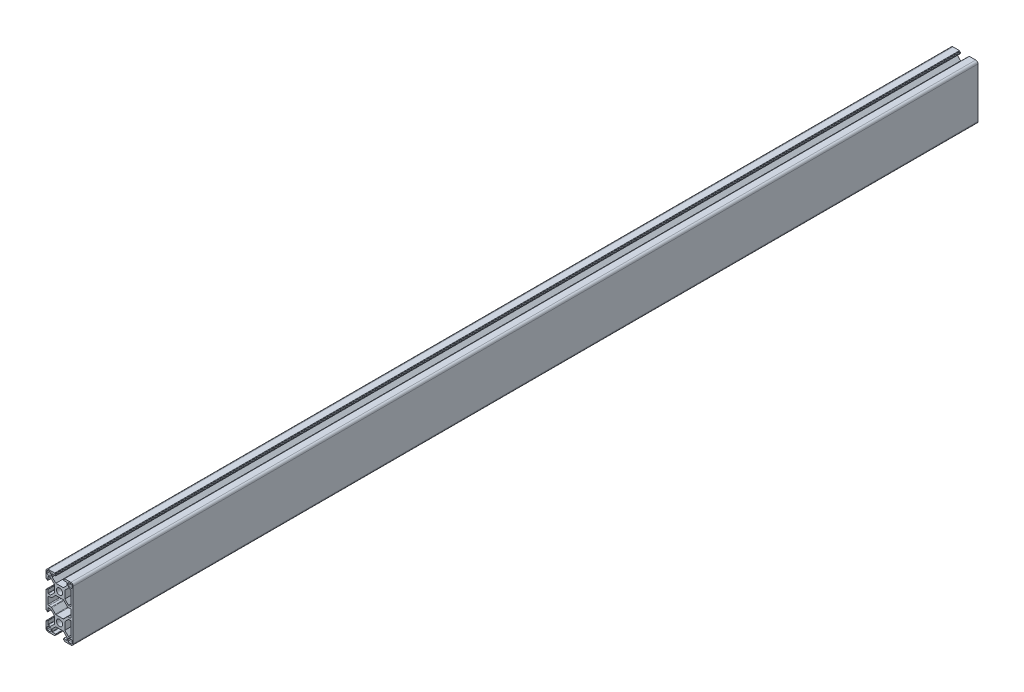
SolidWorks part; units mm, degrees
material "6063 T5"
ref_plane "Спереди" through (0, 0, 0) normal (0, 0, 1) x (1, 0, 0)
ref_plane "Сверху" through (0, 0, 0) normal (0, 1, 0) x (1, 0, 0)
ref_plane "Справа" through (0, 0, 0) normal (1, 0, 0) x (0, 0, -1)
sketch "Эскиз1" plane through (0, 0, 0) normal (0, 0, 1) x (1, 0, 0)
  line L0 (42.4804, 14.8887) -> (42.4804, -45.1113) construction
  line L1 (-15, 8.25) -> (-15, 12.5)
  line L2 (-12.5, 15) -> (-8.25, 15)
  line L3 (8.25, 15) -> (12.5, 15)
  line L4 (15, 12.5) -> (15, 8.25)
  line L5 (12.75, 9.55) -> (10.55, 9.55)
  line L6 (-12.75, 13.75) -> (-10.55, 13.75)
  line L7 (-13.75, 12.75) -> (-13.75, 10.55)
  line L8 (-12.75, 9.55) -> (-10.55, 9.55)
  line L9 (-9.55, 12.75) -> (-9.55, 10.55)
  line L10 (13.75, 12.75) -> (13.75, 10.55)
  line L11 (12.75, 13.75) -> (10.55, 13.75)
  line L12 (9.55, 12.75) -> (9.55, 10.55)
  line L13 (0, 0) -> (0, -30) construction
  line L14 (0, -15) -> (-22.4838, -15) construction
  line L15 (9.55, -42.75) -> (9.55, -40.55)
  line L16 (12.75, -43.75) -> (10.55, -43.75)
  line L17 (13.75, -42.75) -> (13.75, -40.55)
  line L18 (-9.55, -42.75) -> (-9.55, -40.55)
  line L19 (-12.75, -39.55) -> (-10.55, -39.55)
  line L20 (-13.75, -42.75) -> (-13.75, -40.55)
  line L21 (-12.75, -43.75) -> (-10.55, -43.75)
  line L22 (12.75, -39.55) -> (10.55, -39.55)
  line L23 (15, -42.5) -> (15, -38.25)
  line L24 (8.25, -45) -> (12.5, -45)
  line L25 (-12.5, -45) -> (-8.25, -45)
  line L26 (-15, -38.25) -> (-15, -42.5)
  line L27 (-15, -8.25) -> (-15, -21.75)
  line L28 (15, -8.25) -> (15, -21.75)
  line L29 (-12.8, -18.5) -> (-12.8, -11.5)
  line L30 (-11.8, -10.5) -> (-9.4029, -10.5)
  line L31 (-8.6958, -10.2071) -> (-4.5816, -6.0929)
  line L32 (-3.8745, -5.8) -> (3.8745, -5.8)
  line L33 (8.6958, -10.2071) -> (4.5816, -6.0929)
  line L34 (11.8, -10.5) -> (9.4029, -10.5)
  line L35 (12.8, -18.5) -> (12.8, -11.5)
  line L36 (11.8, -19.5) -> (9.4029, -19.5)
  line L37 (8.6958, -19.7929) -> (4.5816, -23.9071)
  line L38 (-3.8745, -24.2) -> (3.8745, -24.2)
  line L39 (-8.6958, -19.7929) -> (-4.5816, -23.9071)
  line L40 (-11.8, -19.5) -> (-9.4029, -19.5)
  line L41 (-20.7769, 14.9626) -> (-20.7769, -45.0374) construction
  line L42 (12.8, -25.6) -> (12.8, -34.4)
  line L43 (15, -24.5) -> (15, -35.5)
  line L44 (12.8, 4.4) -> (12.8, -4.4)
  line L45 (15, 5.5) -> (15, -5.5)
  arc A0 (12.5, 15) -> (15, 12.5) centre (12.5, 12.5) cw
  arc A1 (-15, 12.5) -> (-12.5, 15) centre (-12.5, 12.5) cw
  arc A2 (-13.75, 10.55) -> (-12.75, 9.55) centre (-12.75, 10.55) ccw
  arc A3 (-10.55, 9.55) -> (-9.55, 10.55) centre (-10.55, 10.55) ccw
  arc A4 (-10.55, 13.75) -> (-9.55, 12.75) centre (-10.55, 12.75) cw
  arc A5 (-12.75, 13.75) -> (-13.75, 12.75) centre (-12.75, 12.75) ccw
  arc A6 (10.55, 9.55) -> (9.55, 10.55) centre (10.55, 10.55) cw
  arc A7 (13.75, 10.55) -> (12.75, 9.55) centre (12.75, 10.55) cw
  arc A8 (12.75, 13.75) -> (13.75, 12.75) centre (12.75, 12.75) cw
  arc A9 (10.55, 13.75) -> (9.55, 12.75) centre (10.55, 12.75) ccw
  circle A10 centre (0, 0) radius 3.4
  circle A11 centre (0, -30) radius 3.4
  arc A12 (10.55, -43.75) -> (9.55, -42.75) centre (10.55, -42.75) cw
  arc A13 (12.75, -43.75) -> (13.75, -42.75) centre (12.75, -42.75) ccw
  arc A14 (13.75, -40.55) -> (12.75, -39.55) centre (12.75, -40.55) ccw
  arc A15 (10.55, -39.55) -> (9.55, -40.55) centre (10.55, -40.55) ccw
  arc A16 (-12.75, -43.75) -> (-13.75, -42.75) centre (-12.75, -42.75) cw
  arc A17 (-10.55, -43.75) -> (-9.55, -42.75) centre (-10.55, -42.75) ccw
  arc A18 (-10.55, -39.55) -> (-9.55, -40.55) centre (-10.55, -40.55) cw
  arc A19 (-13.75, -40.55) -> (-12.75, -39.55) centre (-12.75, -40.55) cw
  arc A20 (-15, -42.5) -> (-12.5, -45) centre (-12.5, -42.5) ccw
  arc A21 (12.5, -45) -> (15, -42.5) centre (12.5, -42.5) ccw
  arc A22 (-4.5816, -6.0929) -> (-3.8745, -5.8) centre (-3.8745, -6.8) cw
  arc A23 (-9.4029, -10.5) -> (-8.6958, -10.2071) centre (-9.4029, -9.5) ccw
  arc A24 (-12.8, -11.5) -> (-11.8, -10.5) centre (-11.8, -11.5) cw
  arc A25 (4.5816, -6.0929) -> (3.8745, -5.8) centre (3.8745, -6.8) ccw
  arc A26 (9.4029, -10.5) -> (8.6958, -10.2071) centre (9.4029, -9.5) cw
  arc A27 (12.8, -11.5) -> (11.8, -10.5) centre (11.8, -11.5) ccw
  arc A28 (12.8, -18.5) -> (11.8, -19.5) centre (11.8, -18.5) cw
  arc A29 (9.4029, -19.5) -> (8.6958, -19.7929) centre (9.4029, -20.5) ccw
  arc A30 (4.5816, -23.9071) -> (3.8745, -24.2) centre (3.8745, -23.2) cw
  arc A31 (-4.5816, -23.9071) -> (-3.8745, -24.2) centre (-3.8745, -23.2) ccw
  arc A32 (-9.4029, -19.5) -> (-8.6958, -19.7929) centre (-9.4029, -20.5) cw
  arc A33 (-12.8, -18.5) -> (-11.8, -19.5) centre (-11.8, -18.5) ccw
  point P4 (0, 0)
  point P24 (-9.55, 13.75)
  point P27 (-13.75, 13.75)
  point P77 (0, -30)
  point P100 (0, -5.8)
  point P110 (12.8, -15)
  point P127 (-12.8, -15)
  line B0 (-15, 8.25) -> (-15, 5.5)
  line B1 (-14.7, 5.2) -> (-14.3, 5.2)
  line B2 (-14, 4.9) -> (-14, 4.4)
  line B3 (-13.7, 4.1) -> (-13.1, 4.1)
  line B4 (-12.8, 4.4) -> (-12.8, 7.95)
  line B5 (-12.5, 8.25) -> (-9.85, 8.25)
  line B6 (-9.85, 8.25) -> (-5.8, 4.2)
  line B7 (-5.8, 0) -> (-15, 0) construction
  line B8 (-5.8, -4.2) -> (-5.8, 4.2)
  line B9 (-9.85, -8.25) -> (-5.8, -4.2)
  line B10 (-12.5, -8.25) -> (-9.85, -8.25)
  line B11 (-12.8, -4.4) -> (-12.8, -7.95)
  line B12 (-13.7, -4.1) -> (-13.1, -4.1)
  line B13 (-14, -4.9) -> (-14, -4.4)
  line B14 (-14.7, -5.2) -> (-14.3, -5.2)
  line B15 (-15, -8.25) -> (-15, -5.5)
  arc B16 (-12.8, 7.95) -> (-12.5, 8.25) centre (-12.5, 7.95) cw
  arc B17 (-13.1, 4.1) -> (-12.8, 4.4) centre (-13.1, 4.4) ccw
  arc B18 (-14, 4.4) -> (-13.7, 4.1) centre (-13.7, 4.4) ccw
  arc B19 (-14.3, 5.2) -> (-14, 4.9) centre (-14.3, 4.9) cw
  arc B20 (-15, 5.5) -> (-14.7, 5.2) centre (-14.7, 5.5) ccw
  arc B21 (-15, -5.5) -> (-14.7, -5.2) centre (-14.7, -5.5) cw
  arc B22 (-14.3, -5.2) -> (-14, -4.9) centre (-14.3, -4.9) ccw
  arc B23 (-14, -4.4) -> (-13.7, -4.1) centre (-13.7, -4.4) cw
  arc B24 (-13.1, -4.1) -> (-12.8, -4.4) centre (-13.1, -4.4) cw
  arc B25 (-12.8, -7.95) -> (-12.5, -8.25) centre (-12.5, -7.95) ccw
  line B26 (8.25, 15) -> (5.5, 15)
  line B27 (5.2, 14.7) -> (5.2, 14.3)
  line B28 (4.9, 14) -> (4.4, 14)
  line B29 (4.1, 13.7) -> (4.1, 13.1)
  line B30 (4.4, 12.8) -> (7.95, 12.8)
  line B31 (8.25, 12.5) -> (8.25, 9.85)
  line B32 (8.25, 9.85) -> (4.2, 5.8)
  line B33 (0, 5.8) -> (0, 15) construction
  line B34 (-4.2, 5.8) -> (4.2, 5.8)
  line B35 (-8.25, 9.85) -> (-4.2, 5.8)
  line B36 (-8.25, 12.5) -> (-8.25, 9.85)
  line B37 (-4.4, 12.8) -> (-7.95, 12.8)
  line B38 (-4.1, 13.7) -> (-4.1, 13.1)
  line B39 (-4.9, 14) -> (-4.4, 14)
  line B40 (-5.2, 14.7) -> (-5.2, 14.3)
  line B41 (-8.25, 15) -> (-5.5, 15)
  arc B42 (7.95, 12.8) -> (8.25, 12.5) centre (7.95, 12.5) cw
  arc B43 (4.1, 13.1) -> (4.4, 12.8) centre (4.4, 13.1) ccw
  arc B44 (4.4, 14) -> (4.1, 13.7) centre (4.4, 13.7) ccw
  arc B45 (5.2, 14.3) -> (4.9, 14) centre (4.9, 14.3) cw
  arc B46 (5.5, 15) -> (5.2, 14.7) centre (5.5, 14.7) ccw
  arc B47 (-5.5, 15) -> (-5.2, 14.7) centre (-5.5, 14.7) cw
  arc B48 (-5.2, 14.3) -> (-4.9, 14) centre (-4.9, 14.3) ccw
  arc B49 (-4.4, 14) -> (-4.1, 13.7) centre (-4.4, 13.7) cw
  arc B50 (-4.1, 13.1) -> (-4.4, 12.8) centre (-4.4, 13.1) cw
  arc B51 (-7.95, 12.8) -> (-8.25, 12.5) centre (-7.95, 12.5) ccw
  line B52 (15, -8.25) -> (15, -5.5)
  line B53 (14.7, -5.2) -> (14.3, -5.2)
  line B54 (14, -4.9) -> (14, -4.4)
  line B55 (13.7, -4.1) -> (13.1, -4.1)
  line B56 (12.8, -4.4) -> (12.8, -7.95)
  line B57 (12.5, -8.25) -> (9.85, -8.25)
  line B58 (9.85, -8.25) -> (5.8, -4.2)
  line B59 (5.8, 0) -> (15, 0) construction
  line B60 (5.8, 4.2) -> (5.8, -4.2)
  line B61 (9.85, 8.25) -> (5.8, 4.2)
  line B62 (12.5, 8.25) -> (9.85, 8.25)
  line B63 (12.8, 4.4) -> (12.8, 7.95)
  line B64 (13.7, 4.1) -> (13.1, 4.1)
  line B65 (14, 4.9) -> (14, 4.4)
  line B66 (14.7, 5.2) -> (14.3, 5.2)
  line B67 (15, 8.25) -> (15, 5.5)
  arc B68 (12.8, -7.95) -> (12.5, -8.25) centre (12.5, -7.95) cw
  arc B69 (13.1, -4.1) -> (12.8, -4.4) centre (13.1, -4.4) ccw
  arc B70 (14, -4.4) -> (13.7, -4.1) centre (13.7, -4.4) ccw
  arc B71 (14.3, -5.2) -> (14, -4.9) centre (14.3, -4.9) cw
  arc B72 (15, -5.5) -> (14.7, -5.2) centre (14.7, -5.5) ccw
  arc B73 (15, 5.5) -> (14.7, 5.2) centre (14.7, 5.5) cw
  arc B74 (14.3, 5.2) -> (14, 4.9) centre (14.3, 4.9) ccw
  arc B75 (14, 4.4) -> (13.7, 4.1) centre (13.7, 4.4) cw
  arc B76 (13.1, 4.1) -> (12.8, 4.4) centre (13.1, 4.4) cw
  arc B77 (12.8, 7.95) -> (12.5, 8.25) centre (12.5, 7.95) ccw
  line B78 (8.25, -45) -> (5.5, -45)
  line B79 (5.2, -44.7) -> (5.2, -44.3)
  line B80 (4.9, -44) -> (4.4, -44)
  line B81 (4.1, -43.7) -> (4.1, -43.1)
  line B82 (4.4, -42.8) -> (7.95, -42.8)
  line B83 (8.25, -42.5) -> (8.25, -39.85)
  line B84 (8.25, -39.85) -> (4.2, -35.8)
  line B85 (0, -35.8) -> (0, -45) construction
  line B86 (-4.2, -35.8) -> (4.2, -35.8)
  line B87 (-8.25, -39.85) -> (-4.2, -35.8)
  line B88 (-8.25, -42.5) -> (-8.25, -39.85)
  line B89 (-4.4, -42.8) -> (-7.95, -42.8)
  line B90 (-4.1, -43.7) -> (-4.1, -43.1)
  line B91 (-4.9, -44) -> (-4.4, -44)
  line B92 (-5.2, -44.7) -> (-5.2, -44.3)
  line B93 (-8.25, -45) -> (-5.5, -45)
  arc B94 (7.95, -42.8) -> (8.25, -42.5) centre (7.95, -42.5) ccw
  arc B95 (4.1, -43.1) -> (4.4, -42.8) centre (4.4, -43.1) cw
  arc B96 (4.4, -44) -> (4.1, -43.7) centre (4.4, -43.7) cw
  arc B97 (5.2, -44.3) -> (4.9, -44) centre (4.9, -44.3) ccw
  arc B98 (5.5, -45) -> (5.2, -44.7) centre (5.5, -44.7) cw
  arc B99 (-5.5, -45) -> (-5.2, -44.7) centre (-5.5, -44.7) ccw
  arc B100 (-5.2, -44.3) -> (-4.9, -44) centre (-4.9, -44.3) cw
  arc B101 (-4.4, -44) -> (-4.1, -43.7) centre (-4.4, -43.7) ccw
  arc B102 (-4.1, -43.1) -> (-4.4, -42.8) centre (-4.4, -43.1) ccw
  arc B103 (-7.95, -42.8) -> (-8.25, -42.5) centre (-7.95, -42.5) cw
  line B104 (-15, -38.25) -> (-15, -35.5)
  line B105 (-14.7, -35.2) -> (-14.3, -35.2)
  line B106 (-14, -34.9) -> (-14, -34.4)
  line B107 (-13.7, -34.1) -> (-13.1, -34.1)
  line B108 (-12.8, -34.4) -> (-12.8, -37.95)
  line B109 (-12.5, -38.25) -> (-9.85, -38.25)
  line B110 (-9.85, -38.25) -> (-5.8, -34.2)
  line B111 (-5.8, -30) -> (-15, -30) construction
  line B112 (-5.8, -25.8) -> (-5.8, -34.2)
  line B113 (-9.85, -21.75) -> (-5.8, -25.8)
  line B114 (-12.5, -21.75) -> (-9.85, -21.75)
  line B115 (-12.8, -25.6) -> (-12.8, -22.05)
  line B116 (-13.7, -25.9) -> (-13.1, -25.9)
  line B117 (-14, -25.1) -> (-14, -25.6)
  line B118 (-14.7, -24.8) -> (-14.3, -24.8)
  line B119 (-15, -21.75) -> (-15, -24.5)
  arc B120 (-12.8, -37.95) -> (-12.5, -38.25) centre (-12.5, -37.95) ccw
  arc B121 (-13.1, -34.1) -> (-12.8, -34.4) centre (-13.1, -34.4) cw
  arc B122 (-14, -34.4) -> (-13.7, -34.1) centre (-13.7, -34.4) cw
  arc B123 (-14.3, -35.2) -> (-14, -34.9) centre (-14.3, -34.9) ccw
  arc B124 (-15, -35.5) -> (-14.7, -35.2) centre (-14.7, -35.5) cw
  arc B125 (-15, -24.5) -> (-14.7, -24.8) centre (-14.7, -24.5) ccw
  arc B126 (-14.3, -24.8) -> (-14, -25.1) centre (-14.3, -25.1) cw
  arc B127 (-14, -25.6) -> (-13.7, -25.9) centre (-13.7, -25.6) ccw
  arc B128 (-13.1, -25.9) -> (-12.8, -25.6) centre (-13.1, -25.6) ccw
  arc B129 (-12.8, -22.05) -> (-12.5, -21.75) centre (-12.5, -22.05) cw
  line B130 (15, -21.75) -> (15, -24.5)
  line B131 (14.7, -24.8) -> (14.3, -24.8)
  line B132 (14, -25.1) -> (14, -25.6)
  line B133 (13.7, -25.9) -> (13.1, -25.9)
  line B134 (12.8, -25.6) -> (12.8, -22.05)
  line B135 (12.5, -21.75) -> (9.85, -21.75)
  line B136 (9.85, -21.75) -> (5.8, -25.8)
  line B137 (5.8, -30) -> (15, -30) construction
  line B138 (5.8, -34.2) -> (5.8, -25.8)
  line B139 (9.85, -38.25) -> (5.8, -34.2)
  line B140 (12.5, -38.25) -> (9.85, -38.25)
  line B141 (12.8, -34.4) -> (12.8, -37.95)
  line B142 (13.7, -34.1) -> (13.1, -34.1)
  line B143 (14, -34.9) -> (14, -34.4)
  line B144 (14.7, -35.2) -> (14.3, -35.2)
  line B145 (15, -38.25) -> (15, -35.5)
  arc B146 (12.8, -22.05) -> (12.5, -21.75) centre (12.5, -22.05) ccw
  arc B147 (13.1, -25.9) -> (12.8, -25.6) centre (13.1, -25.6) cw
  arc B148 (14, -25.6) -> (13.7, -25.9) centre (13.7, -25.6) cw
  arc B149 (14.3, -24.8) -> (14, -25.1) centre (14.3, -25.1) ccw
  arc B150 (15, -24.5) -> (14.7, -24.8) centre (14.7, -24.5) cw
  arc B151 (15, -35.5) -> (14.7, -35.2) centre (14.7, -35.5) ccw
  arc B152 (14.3, -35.2) -> (14, -34.9) centre (14.3, -34.9) cw
  arc B153 (14, -34.4) -> (13.7, -34.1) centre (13.7, -34.4) ccw
  arc B154 (13.1, -34.1) -> (12.8, -34.4) centre (13.1, -34.4) ccw
  arc B155 (12.8, -37.95) -> (12.5, -38.25) centre (12.5, -37.95) cw
  dimension "D8" = 6.8
  dimension "D3" = 2.5
  dimension "D7" = 1
  dimension "D14" = 1
  dimension "D1" = 15
  dimension "D2" = 60
  dimension "D4" = 1.3
  dimension "D5" = 1.3
  dimension "D6" = 4.2
  dimension "D9" = 30
  dimension "D10" = 9
  dimension "D11" = 2.2
  dimension "D12" = 18.4
  dimension "D13" = 2.2
  dimension "D15" = 60
sketch_block_instance "Блок1-1"
sketch_block "Блок1" parameters "D6"=0.3, "D1"=16.5, "D2"=8.4, "D3"=9.2, "D4"=45, "D5"=10.4, "D7"=2.2, "D8"=1, "D9"=8.2
sketch_block_instance "Блок1-2"
sketch_block_instance "Блок1-3"
sketch_block_instance "Блок1-4"
sketch_block_instance "Блок1-5"
sketch_block_instance "Блок1-6"
extrude "Бобышка-Вытянуть1" add sketch "Эскиз1" along normal blind 1000 contours B141 B155 B140 B139 B138 B136 B135 B146 B134 B147 B133 B148 B132 B149 B131 B150 B130 L28 B52 B72 B53 B71 B54 B70 B55 B69 B56 B68 B57 B58 B60 B61 B62 B77 B63 B76 B64 B75 B65 B74 B66 B73 B67 L4 A0 L3 B26 B46 B27 B45 B28 | B64 B76 L44 B69 B55 B70 B54 B71 B53 B72 L45 B73 B66 B74 B65 B75 | B154 B142 B153 B143 B152 B144 B151 L43 B150 B131 B149 B132 B148 B133 B147 L42
